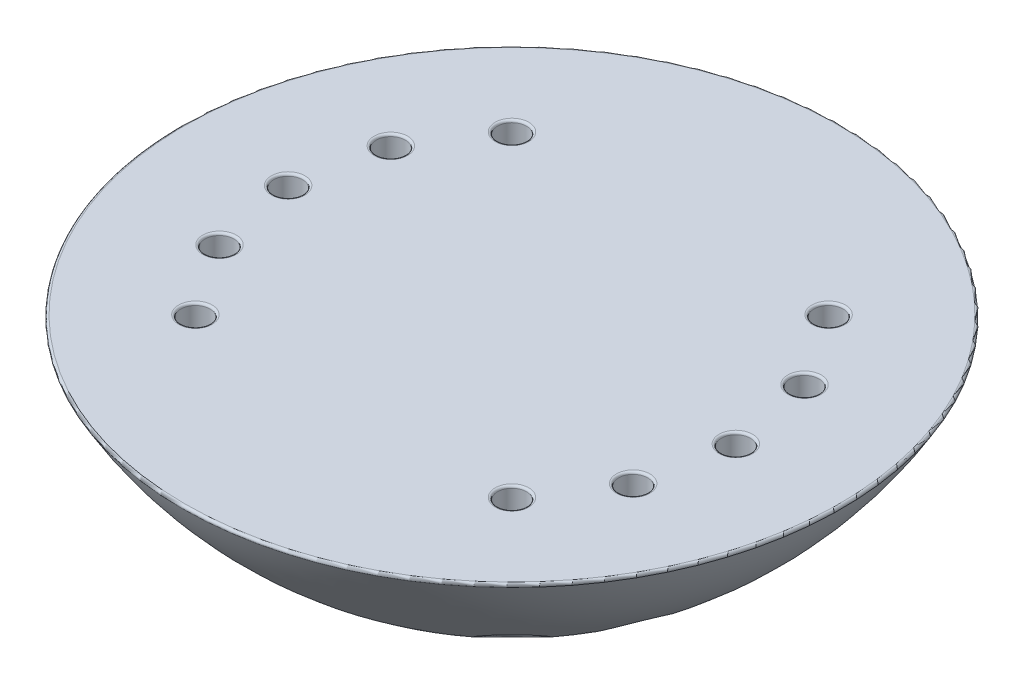
SolidWorks part; units mm, degrees
ref_plane "Front Plane" through (0, 0, 0) normal (0, 0, 1) x (1, 0, 0)
ref_plane "Top Plane" through (0, 0, 0) normal (0, 1, 0) x (1, 0, 0)
ref_plane "Right Plane" through (0, 0, 0) normal (1, 0, 0) x (0, 0, -1)
ref_plane "Bottom Plane" through (0, -250, 0) normal (0, 1, 0) x (1, 0, 0)
ref_plane "End Cut Plane" through (0, 0, 72.5) normal (0, 0, 1) x (1, 0, 0)
sketch "Main Revolve Sketch" plane through (0, 0, 0) normal (0, 0, 1) x (1, 0, 0)
  line L0 (0, 0) -> (0, 13.75)
  line L1 (0, 13.75) -> (0, 96.25)
  line L2 (0, 0) -> (0, -13.75)
  line L3 (-82.5, -13.75) -> (-82.5, 13.75)
  line L4 (0, -13.75) -> (0, -96.25)
  line L5 (-82.5, 0) -> (0, 0) construction
  arc A0 (0, 96.25) -> (-82.5, 13.75) centre (0, 13.75) ccw
  arc A1 (-82.5, -13.75) -> (0, -96.25) centre (0, -13.75) ccw
  dimension "D2" = 82.5
  dimension "D3" = 82.5
  dimension "D1" = 82.5
  dimension "D4" = 13.75
revolve "Main Revolve" add sketch "Main Revolve Sketch" angle 360 about L1
sketch "Top Cut Sketch" plane through (0, 0, 0) normal (0, 1, 0) x (1, 0, 0)
  line L1 (-186.2466, 173.137) -> (257.6713, 173.137)
  line L2 (-186.2466, 173.137) -> (-186.2466, -194.8356)
  line L3 (-186.2466, -194.8356) -> (257.6713, -194.8356)
  line L4 (257.6713, 173.137) -> (257.6713, -194.8356)
extrude "Top Cut" cut sketch "Top Cut Sketch" against normal blind 53.75 and the other way through all
sketch "Bolt Hole Cut Sketch" plane through (0, 0, 0) normal (0, 1, 0) x (1, 0, 0)
  line L0 (-57.5, 0) -> (-40, 0) construction
  circle A0 centre (-48.75, 0) radius 3.1563
  circle A1 centre (0, 0) radius 57.5 construction
  circle A2 centre (0, 0) radius 40 construction
  dimension "D2" = 6.3125
  dimension "D1" = 80
  dimension "D3" = 115
sketch "Bolt Head Cut Sketch" plane through (0, -250, 0) normal (0, 1, 0) x (1, 0, 0)
  line L0 (-57.5, 0) -> (-40, 0) construction
  circle A0 centre (-48.75, 0) radius 5.4375
  circle A1 centre (0, 0) radius 57.5 construction
  circle A2 centre (0, 0) radius 40 construction
  dimension "D2" = 10.875
  dimension "D1" = 115
  dimension "D3" = 80
extrude "Bolt Hole Cut" cut sketch "Bolt Hole Cut Sketch" against normal through all
extrude "Bolt Head Cut" cut sketch "Bolt Head Cut Sketch" along normal offset from surface (186.75 mm away) 9.5 up to face at (-48.75, -53.75, 3.1563)
pattern_circular "CirPattern2" count 3 every 22.5 about axis through (0, 0, 0) along (0, 1, 0) of "Bolt Hole Cut", "Bolt Head Cut"
mirror "Mirror1" about plane through (0, 0, 0) normal (1, 0, 0) of "CirPattern2", "Bolt Hole Cut", "Bolt Head Cut"
sketch "End Cut Sketch" [suppressed] plane through (0, 0, 72.5) normal (0, 0, 1) x (1, 0, 0)
  line L1 (-180.9911, 11.665) -> (163.0254, 11.665)
  line L2 (-180.9911, 11.665) -> (-180.9911, -134.3285)
  line L3 (-180.9911, -134.3285) -> (163.0254, -134.3285)
  line L4 (163.0254, 11.665) -> (163.0254, -134.3285)
extrude "End Cut" [suppressed] cut sketch "End Cut Sketch" along normal through all
pattern_circular "End Cut Circular Pattern" [suppressed] count 4 over 360
fillet "Fillet1" [suppressed] radius 10
fillet "Fillet2" radius 0.5 21 edges at (39.1934, -79.0223, -31.7752) (49.2135, -78.2024, -15.1714) (38.6733, -75.9794, 37.9227) (48.8885, -76.2807, 22.4962) (53.5572, -76.4511, 2.5412) (0, -53.75, 72.1543) (-48.75, -53.75, 3.1563) (-47.3094, -81.1338, 5.2432) (-34.4715, -53.75, -31.3152) (-45.0391, -53.75, -15.4996) (-34.4715, -53.75, 37.6277) (-45.0391, -53.75, 21.8121) (-31.2814, -83.9186, -30.0681) (-41.0731, -83.7226, -14.936) (-31.7752, -79.0223, 39.1934) (-44.615, -78.835, 24.0767) (34.4715, -53.75, -31.3152) (45.0391, -53.75, -15.4996) (34.4715, -53.75, 37.6277) (45.0391, -53.75, 21.8121) (48.75, -53.75, 3.1563)
equation "\"D1@Main Revolve Sketch\" = \"BODY Rad\""
equation "\"D2@Main Revolve Sketch\" = \"BODY Rad\""
equation "\"D3@Main Revolve Sketch\" = \"BODY Rad\""
equation "\"D1@End Cut Plane\" = \"BODY End Cut Rad\""
equation "\"D4@Main Revolve Sketch\" = \"BODY Height Ext\" / 2"
equation "\"D1@Bolt Head Cut\" = \"BODY Bolt Length\" - \"BODY Seal Thickness\" - \"BODY Nut Height\" - \"ALL Nut Size Off\" - \"BODY Wall Extra Thickness\""
equation "\"D2@Bolt Head Cut Sketch\" = \"BODY Bolt Head Dia\" + ( \"ALL Bolt Hole Off\" * \"ALL Horz Bolt Hole Off Scalar\" * 2 )"
equation "\"D1@Top Cut\" = \"BODY Bottom Cut Dist\" + \"BODY Seal Thickness\""
equation "\"D1@Fillet1\" = \"ALL Big Fillet\""
equation "\"D1@Fillet2\" = \"ALL Small Fillet\""
equation "\"D1@Bolt Hole Cut Sketch\"= ( \"BODY End Cut Rad\" * 2 ) - ( \"ARM Rotating Bearing Thickness\" * 2 ) - ( \"BODY Nut Width\" * 2 ) - ( \"BODY Bottom Extra Nut Wall\" * 2 )"
equation "\"D3@Bolt Hole Cut Sketch\"= ( \"BODY End Cut Rad\" * 2 ) - ( \"ARM Rotating Bearing Thickness\" * 2 )"
equation "\"D2@Bolt Hole Cut Sketch\" = \"BODY Bolt Size\" + ( \"ALL Bolt Hole Off\" * \"ALL Horz Bolt Hole Off Scalar\" )"
equation "\"D1@Bolt Head Cut Sketch\" = ( \"BODY End Cut Rad\" * 2 ) - ( \"ARM Rotating Bearing Thickness\" * 2 )"
equation "\"D3@Bolt Head Cut Sketch\" = ( \"BODY End Cut Rad\" * 2 ) - ( \"ARM Rotating Bearing Thickness\" * 2 ) - ( \"BODY Nut Width\" * 2 ) - ( \"BODY Bottom Extra Nut Wall\" * 2 )"
equation "\"End Cut\"= IIF ( \"BODY Height Ext\" > 27.5 , \"unsuppressed\" , \"suppressed\" )"
equation "\"End Cut Sketch\"= IIF ( \"BODY Height Ext\" > 27.5 , \"unsuppressed\" , \"suppressed\" )"
equation "\"End Cut Circular Pattern\"= IIF ( \"BODY Height Ext\" > 27.5 , \"unsuppressed\" , \"suppressed\" )"
equation "\"Fillet1\"= IIF ( \"BODY Height Ext\" > 27.5 , \"unsuppressed\" , \"suppressed\" )"
equation "\"ALL Big Fillet\"= 10.0mm"
equation "\"ALL Medium Fillet\"= 1.0mm"
equation "\"ALL Small Fillet\"= 0.5mm"
equation "\"BODY Rad\"= 82.5mm"
equation "\"BODY End Cut Rad\"= 72.5mm"
equation "\"BODY Height Ext\"= 27.5mm"
equation "\"BODY Bottom Cut Dist\"= 50.0mm"
equation "\"BODY Seal Thickness\"= 3.75mm"
equation "\"BODY Wall Extra Thickness\"= 2.5mm"
equation "\"BODY Bottom Extra Nut Wall\"= 7.5mm"
equation "\"ARM Both Dia\"= 39.75mm"
equation "\"ARM Both Length\"= 67.5mm"
equation "\"ARM Both Wire Hole Dia\"= 15.0mm"
equation "\"ARM Both Prop Seal Thickness\"= 2.5mm"
equation "\"ARM Both Brass Insert Dia\"= 4.875mm"
equation "\"ARM Both Bolt Cut Depth\"= 12.5mm"
equation "\"ARM Both Nema Bolt Off\"= 15.4mm"
equation "\"ARM Both Nema Bolt Depth\"= 2.5mm"
equation "\"ARM Both Nema Width\"= 20.0mm"
equation "\"ARM Both Nema Wall Off\"= 2.5mm"
equation "\"ARM Both Nema Center Dia 1\"= 17.0mm"
equation "\"ARM Both Nema Center Dia 2\"= 10.0mm"
equation "\"ARM Both Nema Bearing OD\"= 16.0mm"
equation "\"ARM Both Nema Bearing ID\"= 10.0mm"
equation "\"ARM Both Nema Bearing Thickness\"= 4.0mm"
equation "\"ARM Both Nema Height\"= 38.0mm"
equation "\"ARM Both Nema Shaft Dia\"= 4.0mm"
equation "\"ARM Both Nema Shaft Length\"= 10.0mm"
equation "\"ARM Both Nema Center Height\"= 1.5mm"
equation "\"ARM Rotating Bearing OD\"= 68.0mm"
equation "\"ARM Rotating Bearing ID\"= 40.0mm"
equation "\"ARM Rotating Bearing Thickness\"= 15.0mm"
equation "\"ARM Static Mount Dia\"= 65.0mm"
equation "\"ARM Static Bolt Off\"= 1.125mm"
equation "\"ALL Bolt Hole Off\"= 0.25mm"
equation "\"ALL Vert Bolt Hole Off Scalar\"= 0.5mm"
equation "\"ALL Horz Bolt Hole Off Scalar\"= 1.25mm"
equation "\"ALL Nut Size Off\"= 0.25mm"
equation "\"ALL Vert Nut Off Scalar\"= 0.5mm"
equation "\"ALL Horz Nut Off Scalar\"= 1.25mm"
equation "\"BODY Bolt Count\"= 12"
equation "\"BODY Bolt Size\"= 6"
equation "\"BODY Bolt Length\"= 22.0mm"
equation "\"BODY Bolt Head Dia\"= IIF ( \"BODY Bolt Size\" = 3 , 5.75mm , IIF ( \"BODY Bolt Size\" = 4 , 7.25mm , IIF ( \"BODY Bolt Size\" = 5 , 8.75mm , IIF ( \"BODY Bolt Size\" = 6 , 10.25mm , 5.75mm ) ) ) )"
equation "\"BODY Bolt Head Height\"= IIF ( \"BODY Bolt Size\" = 3 , 3.0mm , IIF ( \"BODY Bolt Size\" = 4 , 4.0mm , IIF ( \"BODY Bolt Size\" = 5 , 5.0mm , IIF ( \"BODY Bolt Size\" = 6 , 6.0mm , 3.0mm ) ) ) )"
equation "\"BODY Nut Width\"= IIF ( \"BODY Bolt Size\" = 3 , 5.5mm , IIF ( \"BODY Bolt Size\" = 4 , 7.0mm , IIF ( \"BODY Bolt Size\" = 5 , 8.0mm , IIF ( \"BODY Bolt Size\" = 6 , 10.0mm , 5.5mm ) ) ) )"
equation "\"BODY Nut Height\"= IIF ( \"BODY Bolt Size\" = 3 , 4.0mm , IIF ( \"BODY Bolt Size\" = 4 , 5.0mm , IIF ( \"BODY Bolt Size\" = 5 , 5.0mm , IIF ( \"BODY Bolt Size\" = 6 , 6.0mm , 4.0mm ) ) ) )"
equation "\"ARM Static Bolt Count\"= 8"
equation "\"ARM Static Bolt Size\"= 5"
equation "\"ARM Static Bolt Length\"= 20.0mm"
equation "\"ARM Static Bolt Head Dia\"= IIF ( \"ARM Static Bolt Size\" = 3 , 5.75mm , IIF ( \"ARM Static Bolt Size\" = 4 , 7.25mm , IIF ( \"ARM Static Bolt Size\" = 5 , 8.75mm , IIF ( \"ARM Static Bolt Size\" = 6 , 10.25mm , 5.75mm ) ) ) )"
equation "\"ARM Static Bolt Head Height\"= IIF ( \"ARM Static Bolt Size\" = 3 , 3.0mm , IIF ( \"ARM Static Bolt Size\" = 4 , 4.0mm , IIF ( \"ARM Static Bolt Size\" = 5 , 5.0mm , IIF ( \"ARM Static Bolt Size\" = 6 , 6.0mm , 3.0mm ) ) ) )"
equation "\"ARM Static Nut Width\"= IIF ( \"ARM Static Bolt Size\" = 3 , 5.5mm , IIF ( \"ARM Static Bolt Size\" = 4 , 7.0mm , IIF ( \"ARM Static Bolt Size\" = 5 , 8.0mm , IIF ( \"ARM Static Bolt Size\" = 6 , 10.0mm , 5.5mm ) ) ) )"
equation "\"ARM Static Nut Height\"= IIF ( \"ARM Static Bolt Size\" = 3 , 4.0mm , IIF ( \"ARM Static Bolt Size\" = 4 , 5.0mm , IIF ( \"ARM Static Bolt Size\" = 5 , 5.0mm , IIF ( \"ARM Static Bolt Size\" = 6 , 6.0mm , 4.0mm ) ) ) )"
equation "\"ARM Gear Width\"= 10.0mm"
equation "\"ARM Gear Width Off\"= 2.5mm"
equation "\"ARM Gear Bolt Count\"= 4"
equation "\"ARM Gear Rotation\"= 360.0deg"
equation "\"ARM Gear Bolt Size\"= 3"
equation "\"ARM Gear Bolt Length\"= 20.0mm"
equation "\"ARM Gear Bolt Head Dia\"= IIF ( \"ARM Static Bolt Size\" = 3 , 5.75mm , IIF ( \"ARM Static Bolt Size\" = 4 , 7.25mm , IIF ( \"ARM Static Bolt Size\" = 5 , 8.75mm , IIF ( \"ARM Static Bolt Size\" = 6 , 10.25mm , 5.75mm ) ) ) )"
equation "\"ARM Gear Bolt Head Height\"= IIF ( \"ARM Static Bolt Size\" = 3 , 3.0mm , IIF ( \"ARM Static Bolt Size\" = 4 , 4.0mm , IIF ( \"ARM Static Bolt Size\" = 5 , 5.0mm , IIF ( \"ARM Static Bolt Size\" = 6 , 6.0mm , 3.0mm ) ) ) )"
equation "\"ARM Gear Nut Width\"= IIF ( \"ARM Static Bolt Size\" = 3 , 5.5mm , IIF ( \"ARM Static Bolt Size\" = 4 , 7.0mm , IIF ( \"ARM Static Bolt Size\" = 5 , 8.0mm , IIF ( \"ARM Static Bolt Size\" = 6 , 10.0mm , 5.5mm ) ) ) )"
equation "\"ARM Gear Nut Height\"= IIF ( \"ARM Static Bolt Size\" = 3 , 4.0mm , IIF ( \"ARM Static Bolt Size\" = 4 , 5.0mm , IIF ( \"ARM Static Bolt Size\" = 5 , 5.0mm , IIF ( \"ARM Static Bolt Size\" = 6 , 6.0mm , 4.0mm ) ) ) )"
equation "\"ARM Both Prop Plate Bolt Size\"= 3"
equation "\"ARM Both Prop Plate Bolt Length\"= 16.0mm"
equation "\"ARM Both Prop Plate Bolt Head Dia\"= IIF ( \"ARM Both Prop Plate Bolt Size\" = 3 , 5.75mm , IIF ( \"ARM Both Prop Plate Bolt Size\" = 4 , 7.25mm , IIF ( \"ARM Both Prop Plate Bolt Size\" = 5 , 8.75mm , IIF ( \"ARM Both Prop Plate Bolt Size\" = 6 , 10.25mm , 5.75mm ) ) ) )"
equation "\"ARM Both Prop Plate Bolt Head Height\"= IIF ( \"ARM Both Prop Plate Bolt Size\" = 3 , 3.0mm , IIF ( \"ARM Both Prop Plate Bolt Size\" = 4 , 4.0mm , IIF ( \"ARM Both Prop Plate Bolt Size\" = 5 , 5.0mm , IIF ( \"ARM Both Prop Plate Bolt Size\" = 6 , 6.0mm , 3.0mm ) ) ) )"
equation "\"ARM Both Nema Bolt Size\"= 2"
equation "\"ARM Both Nema Bolt Head Dia\"= IIF ( \"ARM Both Nema Bolt Size\" = 3 , 5.75mm , IIF ( \"ARM Both Nema Bolt Size\" = 4 , 7.25mm , IIF ( \"ARM Both Nema Bolt Size\" = 5 , 8.75mm , IIF ( \"ARM Both Nema Bolt Size\" = 6 , 10.25mm , 5.75mm ) ) ) )"
equation "\"ARM Both Nema Bolt Head Height\"= IIF ( \"ARM Both Nema Bolt Size\" = 3 , 3.0mm , IIF ( \"ARM Both Nema Bolt Size\" = 4 , 4.0mm , IIF ( \"ARM Both Nema Bolt Size\" = 5 , 5.0mm , IIF ( \"ARM Both Nema Bolt Size\" = 6 , 6.0mm , 3.0mm ) ) ) )"
